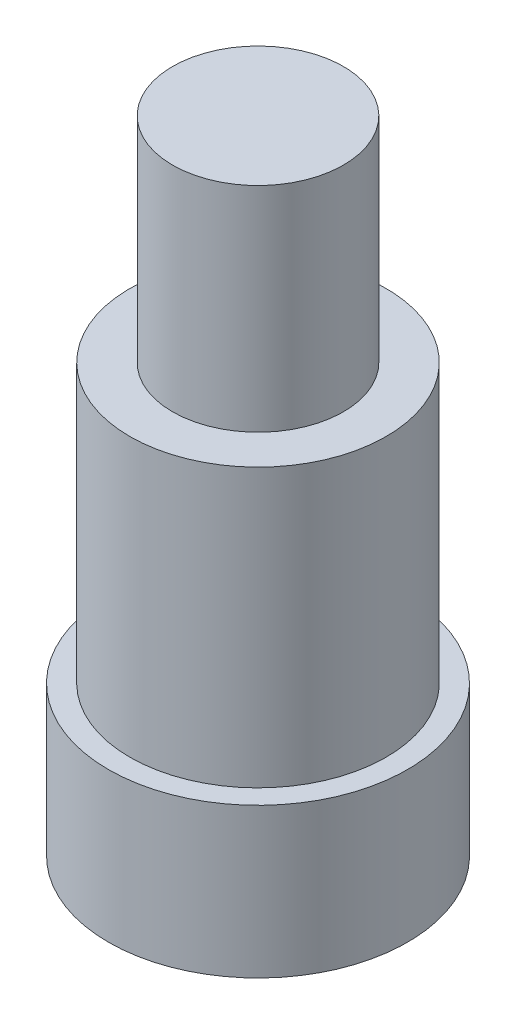
SolidWorks part; units mm, degrees
ref_plane "Front Plane" through (0, 0, 0) normal (0, 0, 1) x (1, 0, 0)
ref_plane "Top Plane" through (0, 0, 0) normal (0, 1, 0) x (1, 0, 0)
ref_plane "Right Plane" through (0, 0, 0) normal (1, 0, 0) x (0, 0, -1)
sketch "Sketch1" plane through (0, 0, 0) normal (0, 1, 0) x (1, 0, 0)
  circle A0 centre (0, 0) radius 7
  dimension "D1" = 14
extrude "Boss-Extrude1" add sketch "Sketch1" along normal blind 7
sketch "Sketch2" plane through (0, 7, 0) normal (0, 1, 0) x (1, 0, 0)
  circle A0 centre (0, 0) radius 6
  dimension "D1" = 12
extrude "Boss-Extrude2" add sketch "Sketch2" along normal blind 13
sketch "Sketch3" plane through (0, 20, 0) normal (0, 1, 0) x (1, 0, 0)
  circle A0 centre (0, 0) radius 4
  dimension "D1" = 8
extrude "Boss-Extrude3" add sketch "Sketch3" along normal blind 10
